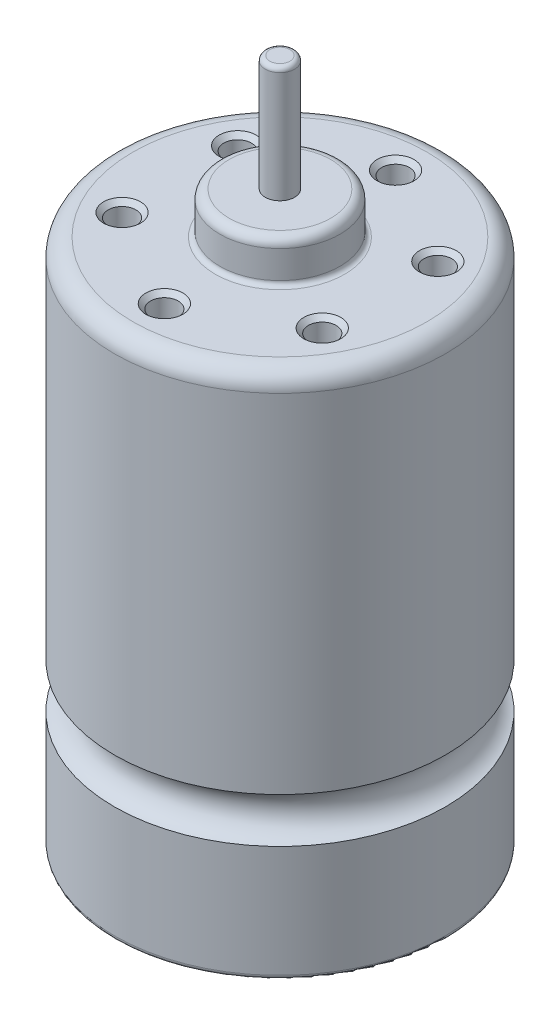
SolidWorks part; units mm, degrees
ref_plane "Front Plane" through (0, 0, 0) normal (0, 0, 1) x (1, 0, 0)
ref_plane "Top Plane" through (0, 0, 0) normal (0, 1, 0) x (1, 0, 0)
ref_plane "Right Plane" through (0, 0, 0) normal (1, 0, 0) x (0, 0, -1)
sketch "Sketch1" plane through (0, 0, 0) normal (0, 1, 0) x (1, 0, 0)
  circle A0 centre (0, 0) radius 17.9
  dimension "D1" = 35.8
extrude "Boss-Extrude1" add sketch "Sketch1" along normal blind 57
sketch "Sketch3" plane through (0, 57, 0) normal (0, 1, 0) x (1, 0, 0)
  circle A0 centre (0, 0) radius 6.5
  dimension "D1" = 13
extrude "Boss-Extrude3" add sketch "Sketch3" along normal blind 4.5
sketch "Sketch4" plane through (0, 57, 0) normal (0, 1, 0) x (1, 0, 0)
  circle A0 centre (0, 0) radius 1.585
  dimension "D1" = 3.17
extrude "Boss-Extrude4" add sketch "Sketch4" along normal blind 17
sketch "Sketch5" plane through (0, 0, 0) normal (0, 0, 1) x (1, 0, 0)
  line L0 (0, 74) -> (0, 0) construction
  line L1 (1.585, 74) -> (-1.585, 74) construction
  line L2 (-18.5, 15) -> (0, 15) construction
  line L3 (-17.9, 0) -> (17.9, 0) construction
  circle A0 centre (-18.5, 15) radius 2.5
  dimension "D1" = 5
  dimension "D2" = 18.5
  dimension "D3" = 15
revolve "Cut-Revolve1" cut sketch "Sketch5" angle 360 about L0
sketch "Sketch6" plane through (0, 0, 0) normal (0, -1, 0) x (1, 0, 0)
  circle A0 centre (0, 0) radius 5.1
  dimension "D1" = 10.2
extrude "Boss-Extrude5" add sketch "Sketch6" along normal blind 3
sketch "Sketch7" plane through (0, -3, 0) normal (0, -1, 0) x (1, 0, 0)
  circle A0 centre (0, 0) radius 1.585
  dimension "D1" = 3.17
extrude "Boss-Extrude6" add sketch "Sketch7" along normal blind 1
sketch "Sketch8" plane through (0, 57, 0) normal (0, 1, 0) x (1, 0, 0)
  line L0 (0, 0) -> (0, -12.5) construction
  circle A1 centre (0, -12.5) radius 1.5
  circle A2 centre (-10.8253, -6.25) radius 1.5
  circle A3 centre (-10.8253, 6.25) radius 1.5
  circle A4 centre (0, 12.5) radius 1.5
  circle A5 centre (10.8253, 6.25) radius 1.5
  circle A6 centre (10.8253, -6.25) radius 1.5
  point P1 (-30.872, -1.8905)
  point P5 (0, 0)
  dimension "D1" = 6
  dimension "D3" = 3
  dimension "D2" = 12.5
extrude "Cut-Extrude1" cut sketch "Sketch8" against normal blind 7
chamfer "Chamfer1" distance 0.5 angle 45 6 edges at (10.8253, 57, -4.75) (10.8253, 57, 7.75) (0, 57, 14) (-10.8253, 57, 7.75) (-10.8253, 57, -4.75) (0, 57, -11)
fillet "Fillet2" radius 1 2 edges at (0, 61.5, 6.5) (0, -3, -5.1)
fillet "Fillet1" radius 2 1 edges at (0, 57, 17.9)
fillet "Fillet3" radius 0.5 4 edges at (0, 0, -5.1) (0, 57, 6.5) (0, 0, 17.9) (0, 74, 1.585)
